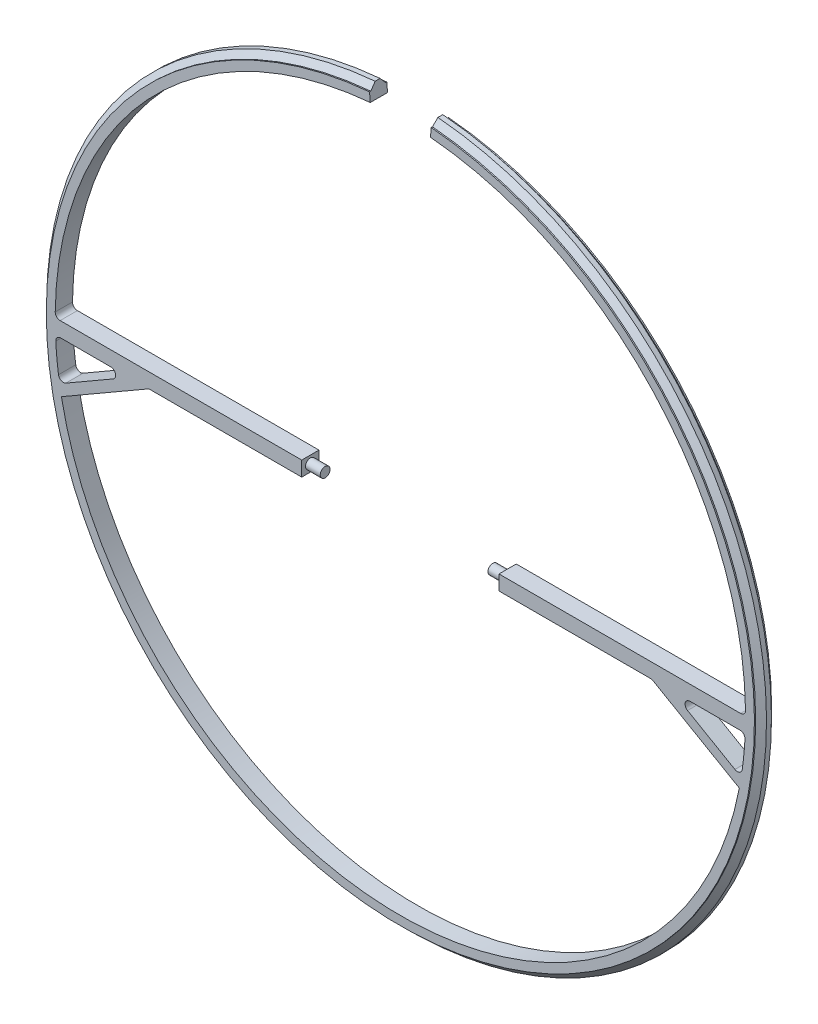
SolidWorks part; units mm, degrees
ref_plane "Front Plane" through (0, 0, 0) normal (0, 0, 1) x (1, 0, 0)
ref_plane "Top Plane" through (0, 0, 0) normal (0, 1, 0) x (1, 0, 0)
ref_plane "Right Plane" through (0, 0, 0) normal (1, 0, 0) x (0, 0, -1)
sketch "Sketch2" plane through (0, 0, 0) normal (1, 0, 0) x (0, 0, -1)
  line L8 (0, 0) -> (50000, 0) construction
  line L9 (1.75, -70) -> (1.75, -71.8)
  line L10 (-1.75, -70) -> (1.75, -70)
  line L11 (-1.75, -71.8) -> (-1.75, -70)
  line L12 (1.5, -71.8) -> (1.75, -71.8)
  line L13 (0.5, -73) -> (1.5, -71.8)
  line L14 (-0.5, -73) -> (0.5, -73)
  line L15 (-1.5, -71.8) -> (-0.5, -73)
  line L16 (-1.75, -71.8) -> (-1.5, -71.8)
  point P0 (0, -73)
  point P1 (0, -70)
  dimension "D1" = 3.5
  dimension "D2" = 1.8
  dimension "D3" = 1.2
  dimension "D4" = 1
  dimension "D5" = 70
  dimension "D6" = 0.25
revolve "Revolve1" add sketch "Sketch2" angle 175 about L8
sketch "Sketch3" plane through (0, 0, 0) normal (0, 0, 1) x (1, 0, 0)
  line L0 (-70, 0) -> (-20, 0)
  line L1 (-20, 0) -> (-20, -3)
  line L2 (-20, -3) -> (-51, -3)
  line L3 (-51, -3) -> (-68.7364, -13.2401)
  line L4 (-55, -3) -> (-69.7364, -11.5081)
  line L5 (-68.7364, -13.2401) -> (-69.7364, -11.5081)
  line L6 (-70, 0) -> (-70, -3)
  line L7 (-55, -3) -> (-70, -3)
  arc A0 (-6.1009, 69.7336) -> (6.1009, 69.7336) centre (0, 0) ccw construction
  dimension "D1" = 2
  dimension "D2" = 3
  dimension "D3" = 50
  dimension "D4" = 15
  dimension "D5" = 30
extrude "Boss-Extrude1" add sketch "Sketch3" along normal up to surface (1.75 mm away) and the other way up to surface (1.75 mm away) up to face at (0, -0.1349, 1.75) other way up to face at (0, -0.1349, -1.75)
sketch "Sketch5" plane through (-20, 0, 0) normal (1, 0, 0) x (0, 0, -1)
  line L0 (1.75, -3) -> (1.75, 0) construction
  line L1 (-1.75, 0) -> (1.75, 0) construction
  circle A0 centre (0, -1.5) radius 1
  point P5 (1.75, -1.5)
  point P8 (0, 0)
  dimension "D1" = 2
extrude "Boss-Extrude2" add sketch "Sketch5" along normal blind 3
fillet "Fillet1" radius 1 5 edges at (-70, 0, 0) (-51, -3, 0) (-55, -3, 0) (-69.1071, -11.1448, 0) (-69.9357, -3, 0)
mirror "Mirror1" about plane through (0, 0, 0) normal (1, 0, 0) of "Fillet1", "Boss-Extrude2", "Boss-Extrude1"
